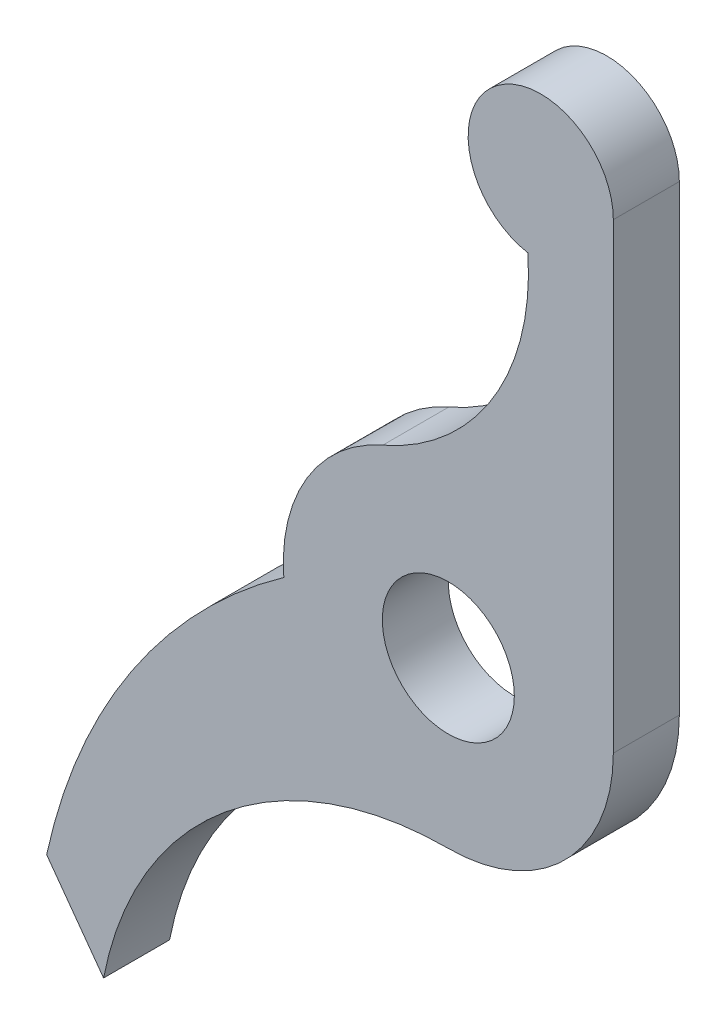
SolidWorks part; units mm, degrees
ref_plane "Front Plane" through (0, 0, 0) normal (0, 0, 1) x (1, 0, 0)
ref_plane "Top Plane" through (0, 0, 0) normal (0, 1, 0) x (1, 0, 0)
ref_plane "Right Plane" through (0, 0, 0) normal (1, 0, 0) x (0, 0, -1)
sketch "Sketch2" plane through (0, 0, 0) normal (0, 0, 1) x (1, 0, 0)
  line L1 (-10.4456, -94.1228) -> (-12.1706, -91.7485)
  line L3 (5, -66.5) -> (5, -80.5)
  line L4 (-10.4456, -94.1228) -> (-11.4618, -92.7242) construction
  circle A0 centre (0, -80.5) radius 5 construction
  arc A1 (-1.9886, -75.9125) -> (-4.9854, -80.8821) centre (0, -80.5) ccw
  arc A2 (0, -85.5) -> (-10.4456, -94.1228) centre (0, -96.1383) ccw
  arc A3 (-12.1706, -91.7485) -> (-4.9854, -80.8821) centre (5.4189, -95.5706) cw
  arc A4 (5, -66.5) -> (2.4102, -68.6652) centre (2.8, -66.5) ccw
  arc A5 (0, -85.5) -> (5, -80.5) centre (0, -80.5) ccw
  arc A6 (2.4102, -68.6652) -> (-1.9886, -75.9125) centre (-4.9055, -69.1835) cw
  dimension "D1" = 18
  dimension "D3" = 2.8
  dimension "D4" = 14
extrude "Boss-Extrude1" add sketch "Sketch2" against normal up to vertex (2 mm away)
sketch "Sketch3" plane through (0, 0, 0) normal (0, 0, 1) x (1, 0, 0)
  circle A0 centre (0, -80.5) radius 2 construction
  circle A1 centre (0, -80.5) radius 2
extrude "Cut-Extrude1" cut sketch "Sketch3" against normal through all
